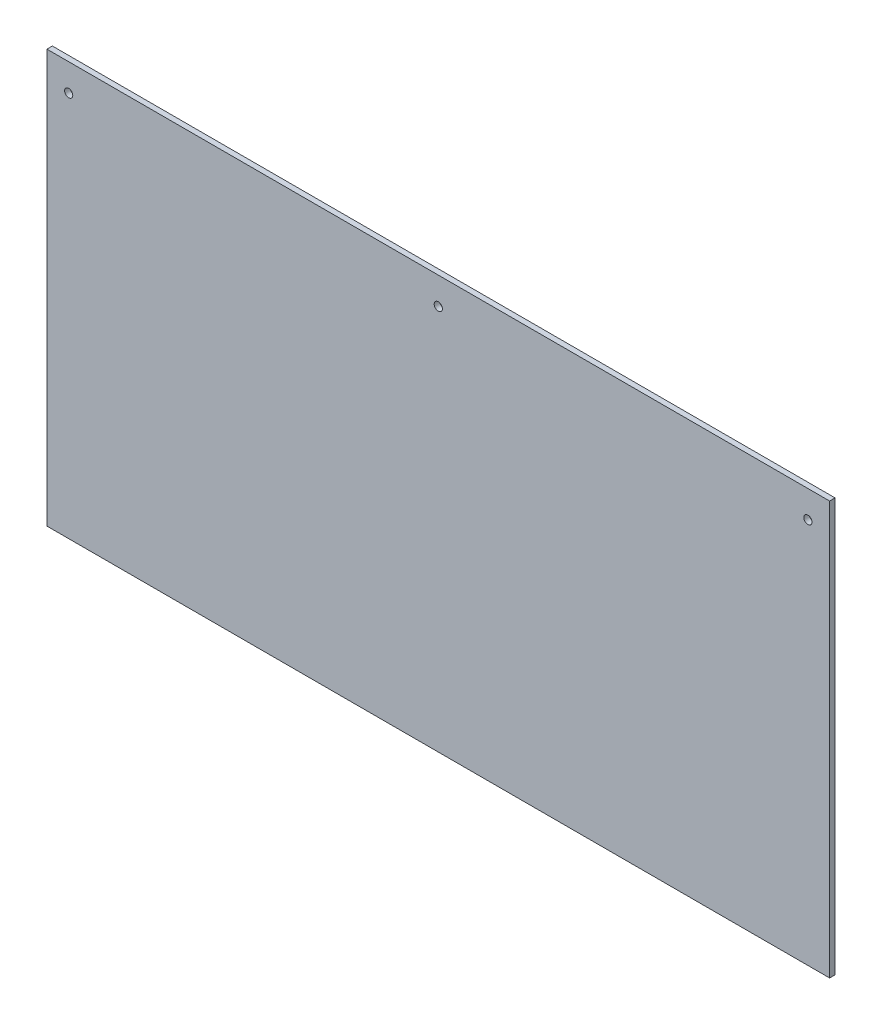
SolidWorks part; units mm, degrees
material "PC High Viscosity"
ref_plane "Front Plane" through (0, 0, 0) normal (0, 0, 1) x (1, 0, 0)
ref_plane "Top Plane" through (0, 0, 0) normal (0, 1, 0) x (1, 0, 0)
ref_plane "Right Plane" through (0, 0, 0) normal (1, 0, 0) x (0, 0, -1)
sketch "Sketch1" plane through (0, 0, 0) normal (0, 0, 1) x (1, 0, 0)
  line L1 (0, 0) -> (914.4, 0)
  line L2 (0, 0) -> (0, 482.6)
  line L3 (0, 482.6) -> (914.4, 482.6)
  line L4 (914.4, 0) -> (914.4, 482.6)
  dimension "D1" = 482.6
  dimension "D2" = 914.4
extrude "Boss-Extrude1" add sketch "Sketch1" along normal blind 6.35
sketch "Sketch2" plane through (0, 0, 6.35) normal (0, 0, 1) x (1, 0, 0)
  line L0 (914.4, 482.6) -> (0, 482.6) construction
  line L1 (0, 482.6) -> (0, 0) construction
  circle A0 centre (25.4, 450.85) radius 4.7625
  dimension "D1" = 9.525
  dimension "D2" = 31.75
  dimension "D3" = 25.4
extrude "Cut-Extrude1" cut sketch "Sketch2" against normal through all
pattern_linear "LPattern1" count 3 spacing 431.8 along (1, 0, 0) of "Cut-Extrude1"
